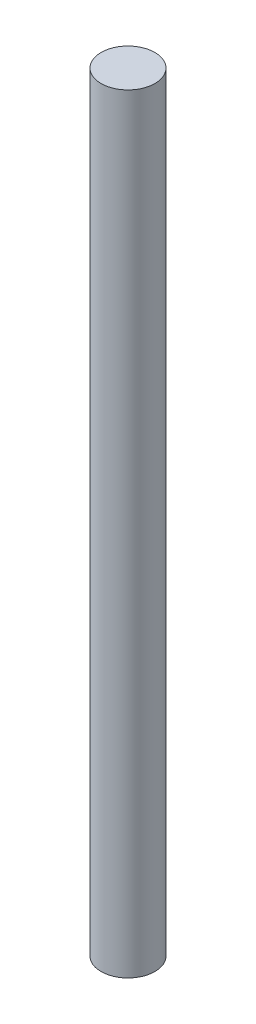
SolidWorks part; units mm, degrees
material "Alloy Steel"
ref_plane "Front Plane" through (0, 0, 0) normal (0, 0, 1) x (1, 0, 0)
ref_plane "Top Plane" through (0, 0, 0) normal (0, 1, 0) x (1, 0, 0)
ref_plane "Right Plane" through (0, 0, 0) normal (1, 0, 0) x (0, 0, -1)
sketch "Sketch1" plane through (0, 0, 0) normal (0, 0, 1) x (1, 0, 0)
  line L3 (-0.7, -20) -> (-0.7, 20)
  line L4 (-0.7, 20) -> (0.7, 20)
  line L5 (0.7, 20) -> (0.7, -20)
  line L8 (-0.7, -20) -> (0.7, -20)
  point P9 (0, -20)
  point P10 (-0.7, 0)
  dimension "D1" = 1.4
  dimension "D2" = 40
revolve "Revolve1" add sketch "Sketch1" angle 360 about L5
